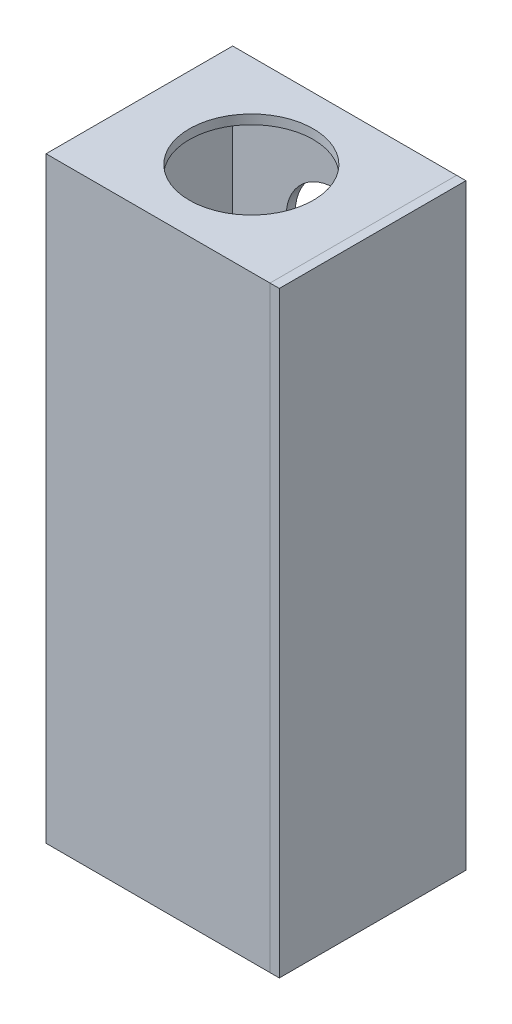
SolidWorks part; units mm, degrees
ref_plane "Front Plane" through (0, 0, 0) normal (0, 0, 1) x (1, 0, 0)
ref_plane "Top Plane" through (0, 0, 0) normal (0, 1, 0) x (1, 0, 0)
ref_plane "Right Plane" through (0, 0, 0) normal (1, 0, 0) x (0, 0, -1)
sketch "Sketch1" plane through (0, 0, 0) normal (0, 1, 0) x (1, 0, 0)
  line L1 (0, 0) -> (76.2, 0)
  line L2 (0, 0) -> (0, 63.5)
  line L3 (0, 63.5) -> (76.2, 63.5)
  line L4 (76.2, 0) -> (76.2, 63.5)
  dimension "D1" = 63.5
  dimension "D2" = 76.2
extrude "Boss-Extrude1" add sketch "Sketch1" along normal blind 203.2
shell "Shell1" thickness 3.175
sketch "Sketch2" plane through (0, 203.2, 0) normal (0, 1, 0) x (1, 0, 0)
  line L0 (76.2, 31.75) -> (0, 31.75) construction
  line L1 (76.2, 0) -> (76.2, 63.5) construction
  line L2 (0, 63.5) -> (0, 0) construction
  circle A0 centre (38.1, 31.75) radius 21.082
  point P8 (0, 0)
  dimension "D1" = 42.164
extrude "Cut-Extrude1" cut sketch "Sketch2" against normal up to next
sketch "Sketch3" plane through (0, 0, -63.5) normal (0, 0, -1) x (-1, 0, 0)
  line L0 (-38.1, 0) -> (-38.1, 203.2) construction
  line L1 (-76.2, 0) -> (0, 0) construction
  line L2 (-76.2, 203.2) -> (0, 203.2) construction
  circle A0 centre (-38.1, 165.1) radius 16.764
  point P8 (0, 0)
  dimension "D1" = 33.528
  dimension "D2" = 165.1
extrude "Cut-Extrude2" cut sketch "Sketch3" against normal up to next
sketch "Sketch4" plane through (0, 0, 0) normal (-1, 0, 0) x (0, 0, 1)
  line L0 (-31.75, 0) -> (-31.75, 203.2) construction
  line L3 (-63.5, 203.2) -> (0, 203.2) construction
  line L4 (-63.5, 0) -> (0, 0) construction
  circle A0 centre (-31.75, 31.75) radius 16.764
  point P4 (-25.4, 101.6)
  point P7 (-25.4, 0)
  point P8 (8.6466, 14.5996)
  dimension "D1" = 33.528
  dimension "D2" = 31.75
extrude "Cut-Extrude3" cut sketch "Sketch4" against normal up to next
sketch "Sketch5" plane through (76.2, 0, 0) normal (1, 0, 0) x (0, 0, -1)
  line L0 (0, 0) -> (63.5, 0) construction
  line L1 (0, 203.2) -> (63.5, 203.2)
  line L2 (0, 203.2) -> (0, 0)
  line L3 (0, 0) -> (63.5, 0)
  line L4 (63.5, 203.2) -> (63.5, 0)
  line L5 (63.5, 203.2) -> (63.5, 0) construction
  point P5 (50.4013, 0)
  point P8 (50.7752, 0)
  point P9 (50.8, 0)
extrude "Boss-Extrude2" add sketch "Sketch5" along normal blind 3.175 separate body
